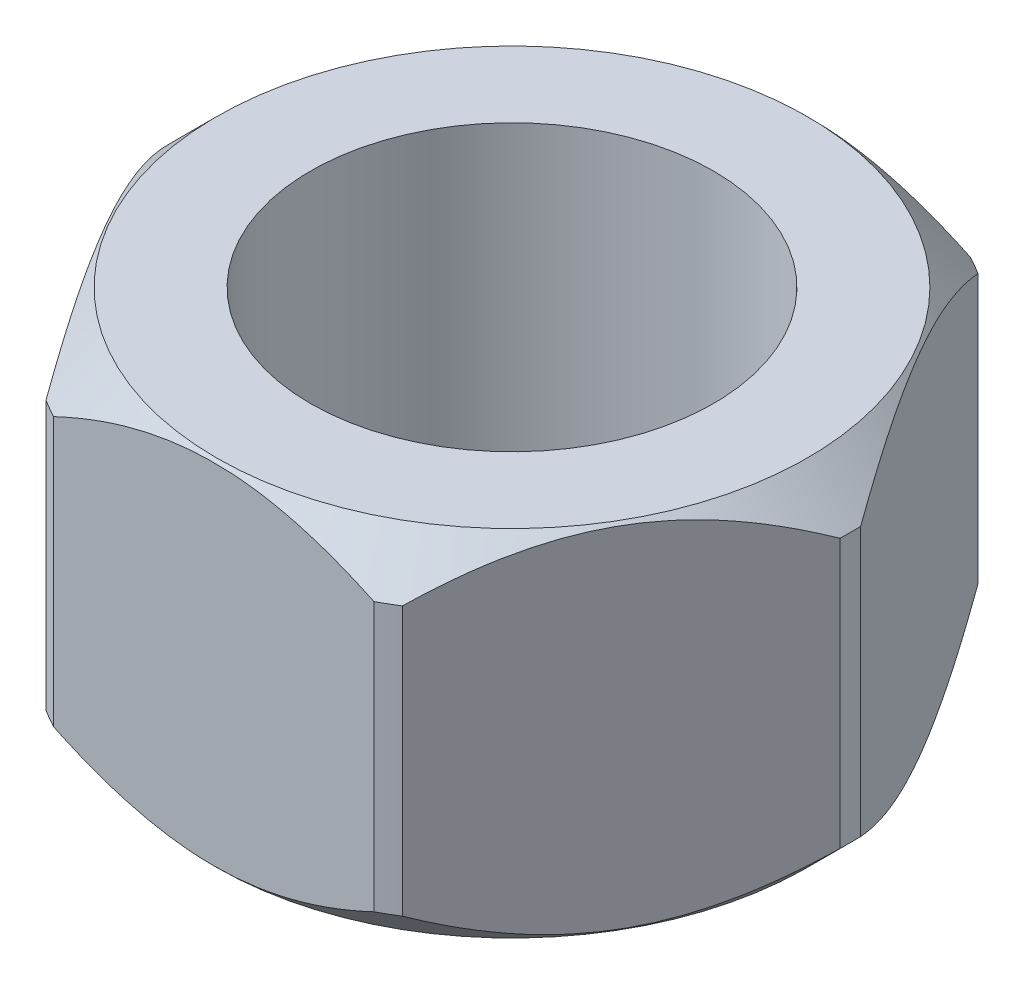
SolidWorks part; units mm, degrees
material "AISI 4130 Steel, normalized at 870C"
ref_plane "Front Plane" through (0, 0, 0) normal (0, 0, 1) x (1, 0, 0)
ref_plane "Top Plane" through (0, 0, 0) normal (0, 1, 0) x (1, 0, 0)
ref_plane "Right Plane" through (0, 0, 0) normal (1, 0, 0) x (0, 0, -1)
sketch "Sketch2" plane through (0, 0, 0) normal (0, 1, 0) x (1, 0, 0)
  circle A0 centre (0, 0) radius 8.001
  dimension "D1" = 16.002
extrude "Extrude2" add sketch "Sketch2" along normal blind 8.382
chamfer "Chamfer1" distance 1.016 angle 45 2 edges at (0, 0, 8.001) (0, 8.382, 8.001)
sketch "Sketch1" plane through (0, 0, 0) normal (0, 1, 0) x (1, 0, 0)
  line L0 (0, 0) -> (10.0707, 0) construction
  line L1 (4.0695, -7.0485) -> (8.1389, 0)
  line L2 (8.1389, 0) -> (4.0695, 7.0485)
  line L3 (4.0695, 7.0485) -> (-4.0695, 7.0485)
  line L4 (-4.0695, 7.0485) -> (-8.1389, 0)
  line L5 (-8.1389, 0) -> (-4.0695, -7.0485)
  line L6 (-4.0695, -7.0485) -> (4.0695, -7.0485)
  circle A0 centre (0, 0) radius 7.0485 construction
  circle A1 centre (0, 0) radius 4.7625
  circle A2 centre (0, 0) radius 8.1389
  dimension "D2" = 9.525
  dimension "D1" = 14.097
extrude "Extrude3" cut sketch "Sketch1" along normal up to next contours L5 A2 | L4 A2 | A1 | L3 A2 | L2 A2 | L1 A2 | L6 A2
